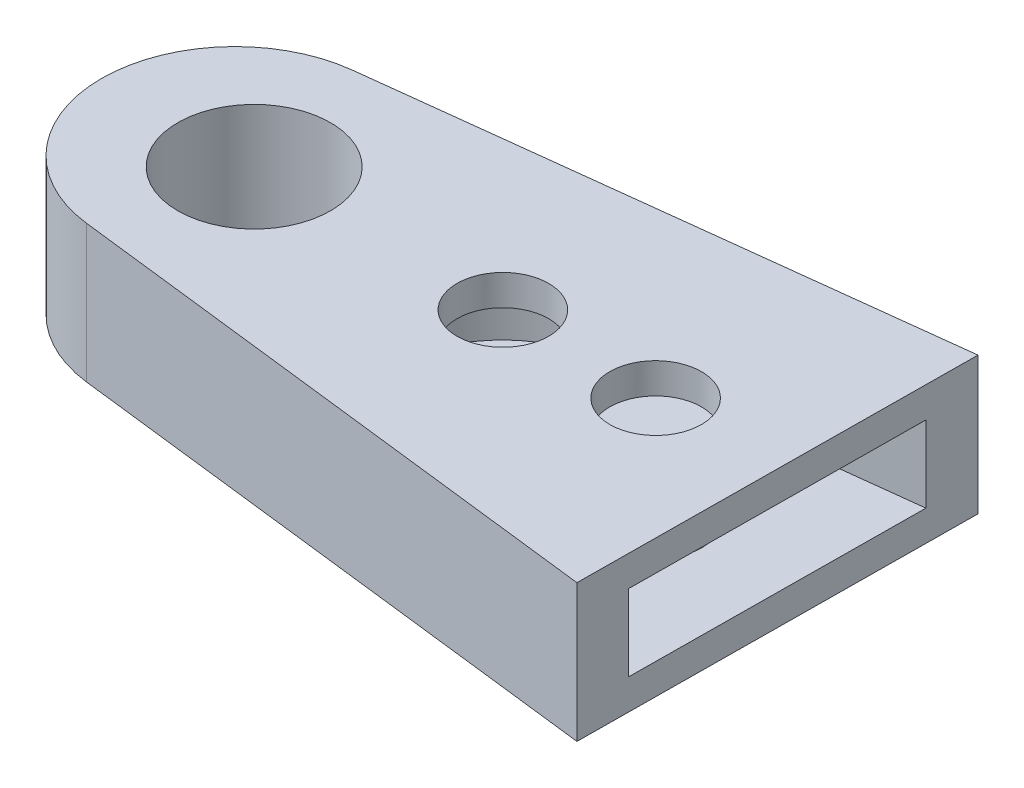
SolidWorks part; units mm, degrees
ref_plane "Front Plane" through (0, 0, 0) normal (0, 0, 1) x (1, 0, 0)
ref_plane "Top Plane" through (0, 0, 0) normal (0, 1, 0) x (1, 0, 0)
ref_plane "Right Plane" through (0, 0, 0) normal (1, 0, 0) x (0, 0, -1)
sketch "Sketch2" plane through (0, 0, 0) normal (0, 1, 0) x (1, 0, 0)
  line L0 (-2.0502, 17.3795) -> (71.2291, 26.024)
  line L1 (-2.0636, -17.3779) -> (70.7763, -26.0276)
  line L2 (71.2291, 26.024) -> (70.7763, -26.0276)
  arc A0 (-2.0502, 17.3795) -> (-2.0636, -17.3779) centre (0, 0) ccw
  dimension "D1" = 35
  dimension "D2" = 13.5
  dimension "D3" = 71
extrude "Boss-Extrude1" add sketch "Sketch2" along normal blind 18
sketch "Sketch3" plane through (70.9973, 0, 0.6176) normal (1, 0, 0.0087) x (0.0087, 0, -1)
  line L0 (-25.4109, 18) -> (26.6427, 18) construction
  line L1 (-18.9109, 14.2) -> (20.1427, 14.2)
  line L2 (-18.9109, 14.2) -> (-18.9109, 3.8)
  line L3 (-18.9109, 3.8) -> (20.1427, 3.8)
  line L4 (20.1427, 14.2) -> (20.1427, 3.8)
  line L5 (-25.4109, 0) -> (26.6427, 0) construction
  line L6 (-25.4109, 18) -> (-25.4109, 0) construction
  line L7 (26.6427, 18) -> (26.6427, 0) construction
  dimension "D1" = 3.8
  dimension "D2" = 3.8
  dimension "D3" = 6.5
  dimension "D4" = 6.5
sketch "Sketch4" plane through (0, 18, 0) normal (0, 1, 0) x (1, 0, 0)
  line L0 (31.503, 14.5867) -> (71.1703, 19.2661)
  line L1 (70.7763, -26.0276) -> (71.2291, 26.024) construction
  line L2 (71.2291, 26.024) -> (-2.0502, 17.3795) construction
  line L3 (32.2251, -14.7411) -> (70.8346, -19.3259)
  line L4 (-2.0636, -17.3779) -> (70.7763, -26.0276) construction
  line L5 (70.8328, -19.5278) -> (71.1725, 19.5243) construction
  line L6 (71.1703, 19.2661) -> (70.8346, -19.3259)
  line L7 (71.1703, 19.2661) -> (70.8346, -19.3259)
  arc A0 (35.0068, 15) -> (34.2454, -14.981) centre (35, 0) ccw
  line M6 (70.7763, -26.0276) -> (71.2291, 26.024)
  dimension "D1" = 30
  dimension "D2" = 0
  dimension "D3" = 0
  dimension "D4" = 0
  dimension "D5" = 36.0013
extrude "Cut-Extrude1" cut sketch "Sketch4" against normal blind 14 contours L0 A0 L3 M6
sketch "Sketch5" plane through (70.9973, 0, 0.6176) normal (1, 0, 0.0087) x (0.0087, 0, -1)
  line L1 (-18.709, 18) -> (19.891, 18)
  line L2 (-18.709, 18) -> (-18.709, 14)
  line L3 (-18.709, 14) -> (19.891, 14)
  line L4 (19.891, 18) -> (19.891, 14)
  dimension "D1" = 4
  dimension "D2" = 38.6
extrude "Boss-Extrude2" add sketch "Sketch5" against normal blind 51.5
sketch "Sketch6" plane through (0, 18, 0) normal (0, 1, 0) x (1, 0, 0)
  circle A0 centre (2.5, 0) radius 10
  arc A4 (-2.0502, 17.3795) -> (-2.0636, -17.3779) centre (0, 0) ccw construction
  point P5 (-17.5, 0.0067)
  dimension "D1" = 20
  dimension "D2" = 20
extrude "Cut-Extrude2" cut sketch "Sketch6" against normal blind 200
sketch "Sketch7" plane through (0, 18, 0) normal (0, 1, 0) x (1, 0, 0)
  line L0 (70.8328, -19.5278) -> (71.1725, 19.5243) construction
  circle A0 centre (35.0018, 0.0534) radius 6
  circle A1 centre (55.0018, 0.0534) radius 6
  dimension "D1" = 12
  dimension "D2" = 36
  dimension "D3" = 12
  dimension "D4" = 20
extrude "Cut-Extrude3" cut sketch "Sketch7" against normal blind 200
